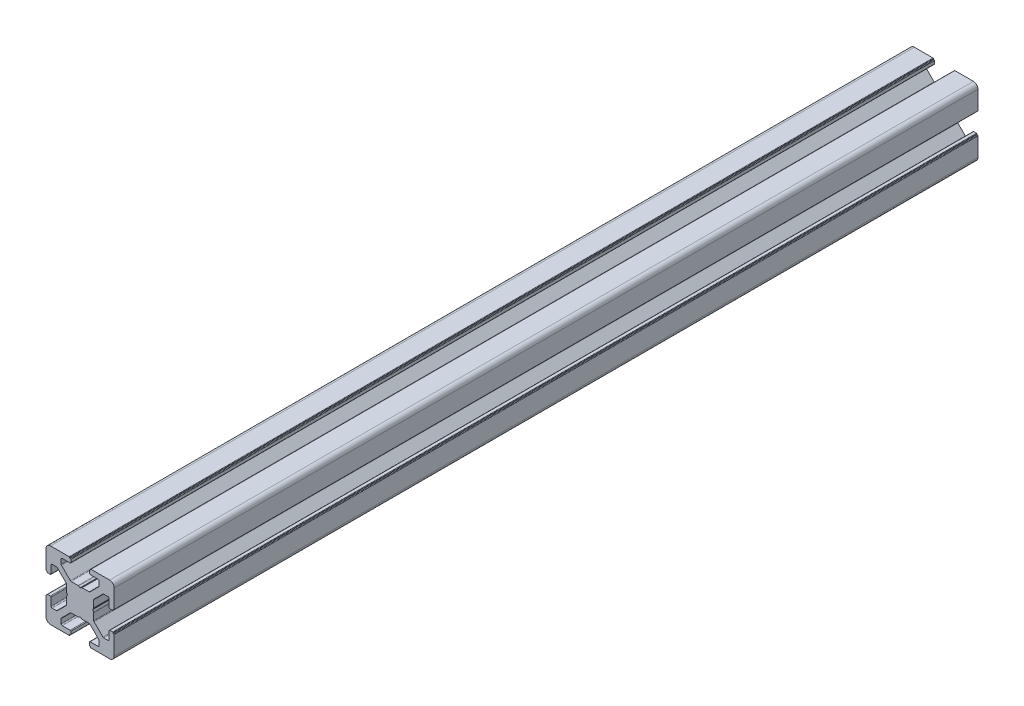
SolidWorks part; units mm, degrees
material "6061 Alloy"
ref_plane "Front Plane" through (0, 0, 0) normal (0, 0, 1) x (1, 0, 0)
ref_plane "Top Plane" through (0, 0, 0) normal (0, 1, 0) x (1, 0, 0)
ref_plane "Right Plane" through (0, 0, 0) normal (1, 0, 0) x (0, 0, -1)
sketch "Sketch1" plane through (0, 0, 0) normal (0, 0, 1) x (1, 0, 0)
  line B0 (-12.8, 4.4) -> (-12.8, 7.85)
  line B1 (-12.3, 8.35) -> (-10.3956, 8.35)
  line B2 (-10.042, 8.2036) -> (-6.1464, 4.308)
  line B3 (-6, 3.9544) -> (-6, 0.934)
  line B4 (-5.933, 0.684) -> (-5.5381, 0)
  line B5 (-5.5381, 0) -> (-5.933, -0.684)
  line B6 (-6, -0.934) -> (-6, -3.9544)
  line B7 (-6.1464, -4.308) -> (-10.042, -8.2036)
  line B8 (-10.3956, -8.35) -> (-12.3, -8.35)
  line B9 (-12.8, -7.85) -> (-12.8, -4.4)
  line B10 (-13.1, -4.1) -> (-14.3, -4.1)
  line B11 (-14.5, -4.3) -> (-14.5, -4.4)
  line B12 (-14.7, -4.6) -> (-14.8, -4.6)
  line B13 (-15, -4.8) -> (-15, -13)
  line B14 (-13, -15) -> (-4.8, -15)
  line B15 (-4.6, -14.8) -> (-4.6, -14.7)
  line B16 (-4.4, -14.5) -> (-4.3, -14.5)
  line B17 (-4.1, -14.3) -> (-4.1, -13.1)
  line B18 (-4.4, -12.8) -> (-7.85, -12.8)
  line B19 (-8.35, -12.3) -> (-8.35, -10.3956)
  line B20 (-8.2036, -10.042) -> (-4.308, -6.1464)
  line B21 (-3.9544, -6) -> (-0.934, -6)
  line B22 (-0.684, -5.933) -> (0, -5.5381)
  line B23 (0, -5.5381) -> (0.684, -5.933)
  line B24 (0.934, -6) -> (3.9544, -6)
  line B25 (4.308, -6.1464) -> (8.2036, -10.042)
  line B26 (8.35, -10.3956) -> (8.35, -12.3)
  line B27 (7.85, -12.8) -> (4.4, -12.8)
  line B28 (4.1, -13.1) -> (4.1, -14.3)
  line B29 (4.3, -14.5) -> (4.4, -14.5)
  line B30 (4.6, -14.7) -> (4.6, -14.8)
  line B31 (4.8, -15) -> (13, -15)
  line B32 (15, -13) -> (15, -4.8)
  line B33 (14.8, -4.6) -> (14.7, -4.6)
  line B34 (14.5, -4.4) -> (14.5, -4.3)
  line B35 (14.3, -4.1) -> (13.1, -4.1)
  line B36 (12.8, -4.4) -> (12.8, -7.85)
  line B37 (12.3, -8.35) -> (10.3956, -8.35)
  line B38 (10.042, -8.2036) -> (6.1464, -4.308)
  line B39 (6, -3.9544) -> (6, -0.934)
  line B40 (5.933, -0.684) -> (5.5381, 0)
  line B41 (5.5381, 0) -> (5.933, 0.684)
  line B42 (6, 0.934) -> (6, 3.9544)
  line B43 (6.1464, 4.308) -> (10.042, 8.2036)
  line B44 (10.3956, 8.35) -> (12.3, 8.35)
  line B45 (12.8, 7.85) -> (12.8, 4.4)
  line B46 (13.1, 4.1) -> (14.3, 4.1)
  line B47 (14.5, 4.3) -> (14.5, 4.4)
  line B48 (14.7, 4.6) -> (14.8, 4.6)
  line B49 (15, 4.8) -> (15, 13)
  line B50 (13, 15) -> (4.8, 15)
  line B51 (4.6, 14.8) -> (4.6, 14.7)
  line B52 (4.4, 14.5) -> (4.3, 14.5)
  line B53 (4.1, 14.3) -> (4.1, 13.1)
  line B54 (4.4, 12.8) -> (7.85, 12.8)
  line B55 (8.35, 12.3) -> (8.35, 10.3956)
  line B56 (8.2036, 10.042) -> (4.308, 6.1464)
  line B57 (3.9544, 6) -> (0.934, 6)
  line B58 (0.684, 5.933) -> (0, 5.5381)
  line B59 (0, 5.5381) -> (-0.684, 5.933)
  line B60 (-0.934, 6) -> (-3.9544, 6)
  line B61 (-4.308, 6.1464) -> (-8.2036, 10.042)
  line B62 (-8.35, 10.3956) -> (-8.35, 12.3)
  line B63 (-7.85, 12.8) -> (-4.4, 12.8)
  line B64 (-4.1, 13.1) -> (-4.1, 14.3)
  line B65 (-4.3, 14.5) -> (-4.4, 14.5)
  line B66 (-4.6, 14.7) -> (-4.6, 14.8)
  line B67 (-4.8, 15) -> (-13, 15)
  line B68 (-15, 13) -> (-15, 4.8)
  line B69 (-14.8, 4.6) -> (-14.7, 4.6)
  line B70 (-14.5, 4.4) -> (-14.5, 4.3)
  line B71 (-14.3, 4.1) -> (-13.1, 4.1)
  arc B72 (-13.1, 4.1) -> (-12.8, 4.4) centre (-13.1, 4.4) ccw
  arc B73 (-12.3, 8.35) -> (-12.8, 7.85) centre (-12.3, 7.85) ccw
  arc B74 (-10.042, 8.2036) -> (-10.3956, 8.35) centre (-10.3956, 7.85) ccw
  arc B75 (-6, 3.9544) -> (-6.1464, 4.308) centre (-6.5, 3.9544) ccw
  arc B76 (-6, 0.934) -> (-5.933, 0.684) centre (-5.5, 0.934) ccw
  arc B77 (-5.933, -0.684) -> (-6, -0.934) centre (-5.5, -0.934) ccw
  arc B78 (-6.1464, -4.308) -> (-6, -3.9544) centre (-6.5, -3.9544) ccw
  arc B79 (-10.3956, -8.35) -> (-10.042, -8.2036) centre (-10.3956, -7.85) ccw
  arc B80 (-12.8, -7.85) -> (-12.3, -8.35) centre (-12.3, -7.85) ccw
  arc B81 (-12.8, -4.4) -> (-13.1, -4.1) centre (-13.1, -4.4) ccw
  arc B82 (-14.3, -4.1) -> (-14.5, -4.3) centre (-14.3, -4.3) ccw
  arc B83 (-14.7, -4.6) -> (-14.5, -4.4) centre (-14.7, -4.4) ccw
  arc B84 (-14.8, -4.6) -> (-15, -4.8) centre (-14.8, -4.8) ccw
  arc B85 (-15, -13) -> (-13, -15) centre (-13, -13) ccw
  arc B86 (-4.8, -15) -> (-4.6, -14.8) centre (-4.8, -14.8) ccw
  arc B87 (-4.4, -14.5) -> (-4.6, -14.7) centre (-4.4, -14.7) ccw
  arc B88 (-4.3, -14.5) -> (-4.1, -14.3) centre (-4.3, -14.3) ccw
  arc B89 (-4.1, -13.1) -> (-4.4, -12.8) centre (-4.4, -13.1) ccw
  arc B90 (-8.35, -12.3) -> (-7.85, -12.8) centre (-7.85, -12.3) ccw
  arc B91 (-8.2036, -10.042) -> (-8.35, -10.3956) centre (-7.85, -10.3956) ccw
  arc B92 (-3.9544, -6) -> (-4.308, -6.1464) centre (-3.9544, -6.5) ccw
  arc B93 (-0.934, -6) -> (-0.684, -5.933) centre (-0.934, -5.5) ccw
  arc B94 (0.684, -5.933) -> (0.934, -6) centre (0.934, -5.5) ccw
  arc B95 (4.308, -6.1464) -> (3.9544, -6) centre (3.9544, -6.5) ccw
  arc B96 (8.35, -10.3956) -> (8.2036, -10.042) centre (7.85, -10.3956) ccw
  arc B97 (7.85, -12.8) -> (8.35, -12.3) centre (7.85, -12.3) ccw
  arc B98 (4.4, -12.8) -> (4.1, -13.1) centre (4.4, -13.1) ccw
  arc B99 (4.1, -14.3) -> (4.3, -14.5) centre (4.3, -14.3) ccw
  arc B100 (4.6, -14.7) -> (4.4, -14.5) centre (4.4, -14.7) ccw
  arc B101 (4.6, -14.8) -> (4.8, -15) centre (4.8, -14.8) ccw
  arc B102 (13, -15) -> (15, -13) centre (13, -13) ccw
  arc B103 (15, -4.8) -> (14.8, -4.6) centre (14.8, -4.8) ccw
  arc B104 (14.5, -4.4) -> (14.7, -4.6) centre (14.7, -4.4) ccw
  arc B105 (14.5, -4.3) -> (14.3, -4.1) centre (14.3, -4.3) ccw
  arc B106 (13.1, -4.1) -> (12.8, -4.4) centre (13.1, -4.4) ccw
  arc B107 (12.3, -8.35) -> (12.8, -7.85) centre (12.3, -7.85) ccw
  arc B108 (10.042, -8.2036) -> (10.3956, -8.35) centre (10.3956, -7.85) ccw
  arc B109 (6, -3.9544) -> (6.1464, -4.308) centre (6.5, -3.9544) ccw
  arc B110 (6, -0.934) -> (5.933, -0.684) centre (5.5, -0.934) ccw
  arc B111 (5.933, 0.684) -> (6, 0.934) centre (5.5, 0.934) ccw
  arc B112 (6.1464, 4.308) -> (6, 3.9544) centre (6.5, 3.9544) ccw
  arc B113 (10.3956, 8.35) -> (10.042, 8.2036) centre (10.3956, 7.85) ccw
  arc B114 (12.8, 7.85) -> (12.3, 8.35) centre (12.3, 7.85) ccw
  arc B115 (12.8, 4.4) -> (13.1, 4.1) centre (13.1, 4.4) ccw
  arc B116 (14.3, 4.1) -> (14.5, 4.3) centre (14.3, 4.3) ccw
  arc B117 (14.7, 4.6) -> (14.5, 4.4) centre (14.7, 4.4) ccw
  arc B118 (14.8, 4.6) -> (15, 4.8) centre (14.8, 4.8) ccw
  arc B119 (15, 13) -> (13, 15) centre (13, 13) ccw
  arc B120 (4.8, 15) -> (4.6, 14.8) centre (4.8, 14.8) ccw
  arc B121 (4.4, 14.5) -> (4.6, 14.7) centre (4.4, 14.7) ccw
  arc B122 (4.3, 14.5) -> (4.1, 14.3) centre (4.3, 14.3) ccw
  arc B123 (4.1, 13.1) -> (4.4, 12.8) centre (4.4, 13.1) ccw
  arc B124 (8.35, 12.3) -> (7.85, 12.8) centre (7.85, 12.3) ccw
  arc B125 (8.2036, 10.042) -> (8.35, 10.3956) centre (7.85, 10.3956) ccw
  arc B126 (3.9544, 6) -> (4.308, 6.1464) centre (3.9544, 6.5) ccw
  arc B127 (0.934, 6) -> (0.684, 5.933) centre (0.934, 5.5) ccw
  arc B128 (-0.684, 5.933) -> (-0.934, 6) centre (-0.934, 5.5) ccw
  arc B129 (-4.308, 6.1464) -> (-3.9544, 6) centre (-3.9544, 6.5) ccw
  arc B130 (-8.35, 10.3956) -> (-8.2036, 10.042) centre (-7.85, 10.3956) ccw
  arc B131 (-7.85, 12.8) -> (-8.35, 12.3) centre (-7.85, 12.3) ccw
  arc B132 (-4.4, 12.8) -> (-4.1, 13.1) centre (-4.4, 13.1) ccw
  arc B133 (-4.1, 14.3) -> (-4.3, 14.5) centre (-4.3, 14.3) ccw
  arc B134 (-4.6, 14.7) -> (-4.4, 14.5) centre (-4.4, 14.7) ccw
  arc B135 (-4.6, 14.8) -> (-4.8, 15) centre (-4.8, 14.8) ccw
  arc B136 (-13, 15) -> (-15, 13) centre (-13, 13) ccw
  arc B137 (-15, 4.8) -> (-14.8, 4.6) centre (-14.8, 4.8) ccw
  arc B138 (-14.5, 4.4) -> (-14.7, 4.6) centre (-14.7, 4.4) ccw
  arc B139 (-14.5, 4.3) -> (-14.3, 4.1) centre (-14.3, 4.3) ccw
sketch_block_instance "Frame30-1"
sketch_block "Frame30"
extrude "Boss-Extrude1" add sketch "Sketch1" along normal blind 380
